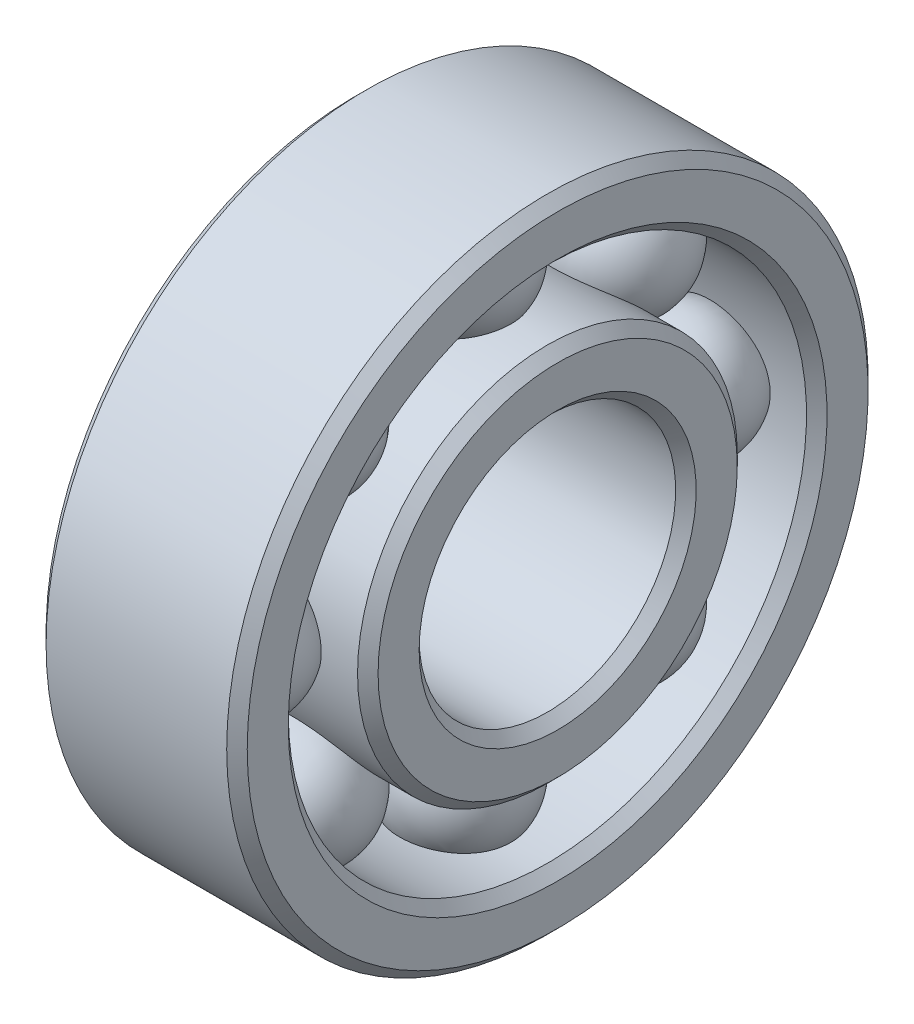
SolidWorks part; units mm, degrees
material "Alloy Steel"
ref_plane "Front Plane" through (0, 0, 0) normal (0, 0, 1) x (1, 0, 0)
ref_plane "Top Plane" through (0, 0, 0) normal (0, 1, 0) x (1, 0, 0)
ref_plane "Right Plane" through (0, 0, 0) normal (1, 0, 0) x (0, 0, -1)
sketch "Sketch1" plane through (0, 0, 0) normal (0, 0, 1) x (1, 0, 0)
  line L0 (0, 0) -> (19.7388, 0) construction
  line L1 (-2.4892, 3.175) -> (2.4892, 3.175)
  line L2 (0, 3.175) -> (0, 0) construction
  line L3 (-2.4892, 7.9375) -> (2.4892, 7.9375)
  line L4 (-2.4892, 6.4135) -> (2.4892, 6.4135)
  line L5 (2.4892, 6.4135) -> (2.4892, 7.9375)
  line L6 (-2.4892, 7.9375) -> (-2.4892, 6.4135)
  line L7 (-2.4892, 3.175) -> (-2.4892, 4.699)
  line L8 (-2.4892, 4.699) -> (2.4892, 4.699)
  line L9 (2.4892, 4.699) -> (2.4892, 3.175)
  line L10 (0, 6.4135) -> (0, 4.699) construction
  circle A0 centre (0, 5.5563) radius 1.9812 construction
  dimension "D4" = 3.9624
  dimension "D1" = 6.35
  dimension "D2" = 15.875
  dimension "D3" = 4.9784
  dimension "D5" = 1.524
revolve "Revolve1" add sketch "Sketch1" angle 360 about L0
sketch "Sketch2" plane through (0, 0, 0) normal (0, 0, 1) x (1, 0, 0)
  line L0 (-1.5875, 5.5563) -> (1.5875, 5.5563)
  arc A1 (1.5875, 5.5563) -> (-1.5875, 5.5563) centre (0, 5.5563) ccw
  dimension "D1" = 3.175
revolve "Revolve2" add sketch "Sketch2" angle 360 about L0
pattern_circular "CirPattern1" count 8 over 360 about axis through (0, 0, 0) along (1, 0, 0) of "Revolve2"
chamfer "Chamfer1" distance 0.254 angle 45 8 edges at (2.4892, 0, 3.175) (2.4892, 0, 4.699) (2.4892, 0, 6.4135) (2.4892, 0, 7.9375) (-2.4892, 0, 4.699) (-2.4892, 0, 3.175) (-2.4892, 0, 7.9375) (-2.4892, 0, 6.4135)
